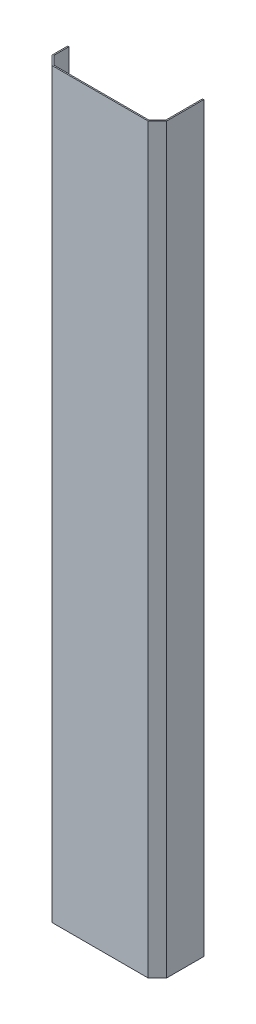
SolidWorks part; units mm, degrees
ref_plane "Front Plane" through (0, 0, 0) normal (0, 0, 1) x (1, 0, 0)
ref_plane "Top Plane" through (0, 0, 0) normal (0, 1, 0) x (1, 0, 0)
ref_plane "Right Plane" through (0, 0, 0) normal (1, 0, 0) x (0, 0, -1)
sketch "Sketch1" plane through (0, 0, 0) normal (0, 1, 0) x (1, 0, 0)
  line L0 (15.8284, 2) -> (2, 15.8284)
  line L1 (0, 0) -> (2, 0)
  line L2 (0, 15) -> (0, 40)
  line L3 (0, 40) -> (2, 40)
  line L4 (2, 15.8284) -> (2, 40)
  line L5 (0, 0) -> (2, 40) construction
  line L6 (0, 40) -> (2, 0) construction
  line L7 (15, 0) -> (170, 0)
  line L8 (0, 0) -> (0, 2)
  line L9 (15.8284, 2) -> (169.1716, 2)
  line L10 (185, 0) -> (185, 2)
  line L11 (0, 0) -> (185, 2) construction
  line L12 (0, 2) -> (185, 0) construction
  line L13 (185, 0) -> (183, 0)
  line L14 (185, 15) -> (185, 75)
  line L15 (185, 75) -> (183, 75)
  line L16 (183, 15.8284) -> (183, 75)
  line L17 (185, 0) -> (183, 75) construction
  line L18 (185, 75) -> (183, 0) construction
  line L19 (15, 0) -> (0, 15)
  line L21 (170, 0) -> (185, 15)
  line L22 (16.4142, 1.4142) -> (1.4142, 16.4142) construction
  line L25 (169.1716, 2) -> (183, 15.8284)
  point P4 (1, 20)
  point P9 (92.5, 1)
  point P13 (184, 37.5)
  point P16 (2, 2)
  point P21 (183, 2)
  dimension "D1" = 2
  dimension "D2" = 2
  dimension "D3" = 2
  dimension "D4" = 40
  dimension "D5" = 185
  dimension "D6" = 75
  dimension "D7" = 2
extrude "Boss-Extrude1" add sketch "Sketch1" along normal blind 1200 contours L7 L16 L9 L4
sketch "Sketch2" plane through (0, 0, 0) normal (-1, 0, 0) x (0, 0, 1)
  line L0 (-40, 1200) -> (-40, 0) construction
  line L1 (-40, 220) -> (-20, 220)
  line L2 (-40, 220) -> (-40, 180)
  line L3 (-40, 180) -> (-20, 180)
  line L4 (-20, 220) -> (-20, 180)
  line L5 (-40, 220) -> (-20, 180) construction
  line L6 (-40, 180) -> (-20, 220) construction
  line L9 (-40, 1155) -> (-20, 1155)
  line L10 (-40, 1155) -> (-40, 1115)
  line L11 (-40, 1115) -> (-20, 1115)
  line L12 (-20, 1155) -> (-20, 1115)
  line L13 (-40, 1155) -> (-20, 1115) construction
  line L14 (-40, 1115) -> (-20, 1155) construction
  line L15 (-15, 1200) -> (-40, 1200) construction
  point P4 (-30, 200)
  point P7 (0, 0)
  point P13 (-30, 1135)
  point P16 (-27.5, 1200)
  dimension "D1" = 40
  dimension "D2" = 85
  dimension "D3" = 40
  dimension "D4" = 1020
  dimension "D5" = 20
  dimension "D6" = 20
extrude "Cut-Extrude1" cut sketch "Sketch2" against normal up to next
